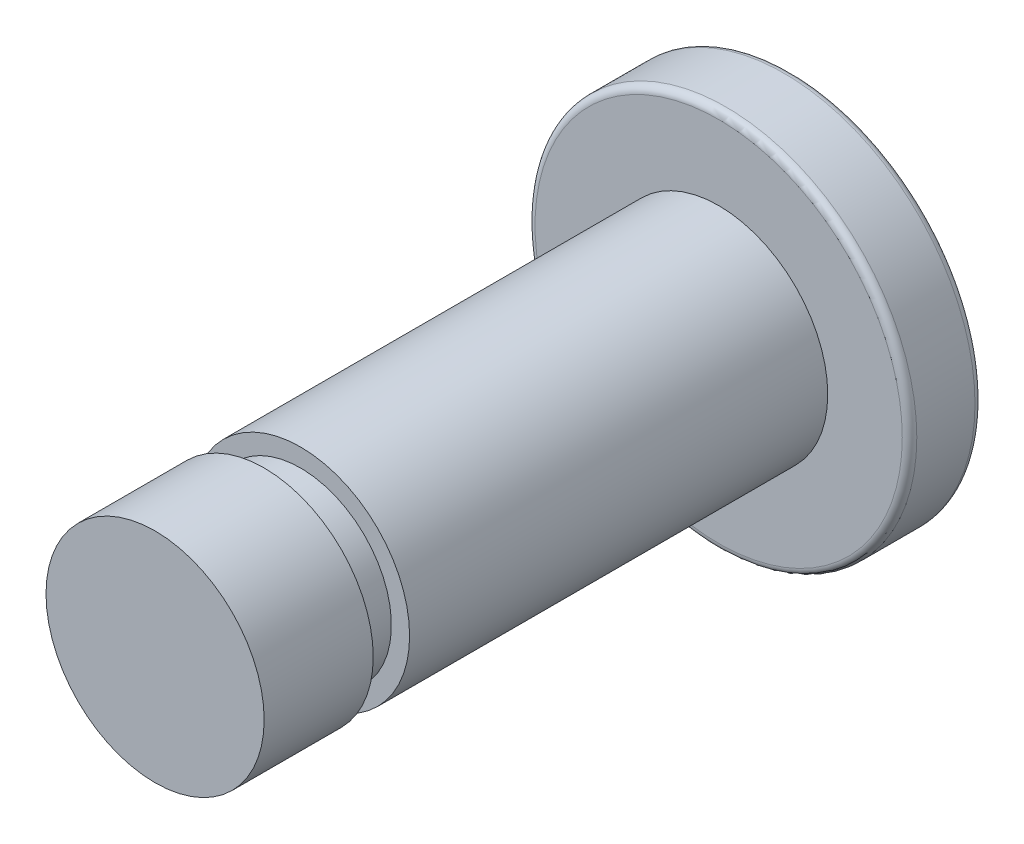
SolidWorks part; units mm, degrees
ref_plane "Alzado" through (0, 0, 0) normal (0, 0, 1) x (1, 0, 0)
ref_plane "Planta" through (0, 0, 0) normal (0, 1, 0) x (1, 0, 0)
ref_plane "Vista lateral" through (0, 0, 0) normal (1, 0, 0) x (0, 0, -1)
sketch "Croquis2" plane through (0, 0, 0) normal (0, 1, 0) x (1, 0, 0)
  line L0 (0, 0) -> (0, 3)
  line L1 (0, 15.5) -> (-2.25, 15.5)
  line L2 (-2.25, 15.5) -> (-2.25, 17.5)
  line L3 (-2.25, 17.5) -> (3, 17.5)
  line L4 (3, 17.5) -> (3, 0)
  line L5 (3, 0) -> (0, 0)
  line L6 (0, 4) -> (0.5, 4)
  line L7 (0.5, 4) -> (0.5, 3)
  line L8 (0.5, 3) -> (0, 3)
  line L9 (0, 4) -> (0, 15.5)
  dimension "D1" = 2
  dimension "D2" = 15.5
  dimension "D3" = 3
  dimension "D4" = 5.25
  dimension "D5" = 3
  dimension "D6" = 1
  dimension "D7" = 0.5
revolve "Revolución1" add sketch "Croquis2" angle 360 about L4
fillet "Redondeo1" radius 0.2 2 edges at (-2.25, 0, -15.5) (-2.25, 0, -17.5)
